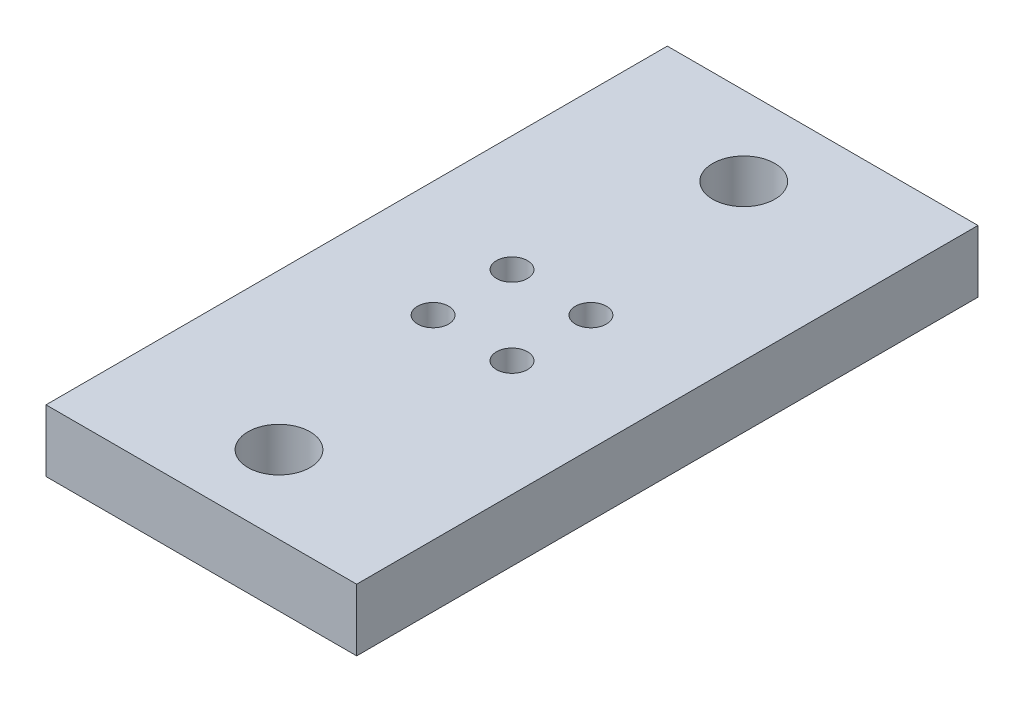
SolidWorks part; units mm, degrees
ref_plane "Alzado" through (0, 0, 0) normal (0, 0, 1) x (1, 0, 0)
ref_plane "Planta" through (0, 0, 0) normal (0, 1, 0) x (1, 0, 0)
ref_plane "Vista lateral" through (0, 0, 0) normal (1, 0, 0) x (0, 0, -1)
sketch "Croquis1" plane through (0, 0, 0) normal (0, 1, 0) x (1, 0, 0)
  line L1 (-5, -10) -> (5, -10)
  line L2 (-5, -10) -> (-5, 10)
  line L3 (-5, 10) -> (5, 10)
  line L4 (5, -10) -> (5, 10)
  line L5 (-5, -10) -> (5, 10) construction
  line L6 (-5, 10) -> (5, -10) construction
  point P0 (0, 0)
extrude "Saliente-Extruir1" add sketch "Croquis1" along normal blind 2
sketch "Croquis2" plane through (0, 2, 0) normal (0, 1, 0) x (1, 0, 0)
  line L0 (0, 0) -> (0, -10) construction
  line L5 (-1.27, -1.27) -> (1.27, 1.27) construction
  line L6 (-1.27, 1.27) -> (1.27, -1.27) construction
  line L7 (-5, -10) -> (5, -10) construction
  line L8 (0, -10) -> (0, -7.5) construction
  line L9 (0, -7.5) -> (0, 10) construction
  line L10 (5, 10) -> (-5, 10) construction
  line L11 (0, 10) -> (0, 7.46) construction
  circle A0 centre (0, 7.46) radius 1
  circle A1 centre (0, -7.5) radius 1
  circle A2 centre (1.27, 1.27) radius 0.5
  circle A3 centre (-1.27, 1.27) radius 0.5
  circle A4 centre (-1.27, -1.27) radius 0.5
  circle A5 centre (1.27, -1.27) radius 0.5
  point P0 (0, 0)
extrude "Cortar-Extruir1" cut sketch "Croquis2" against normal through all
